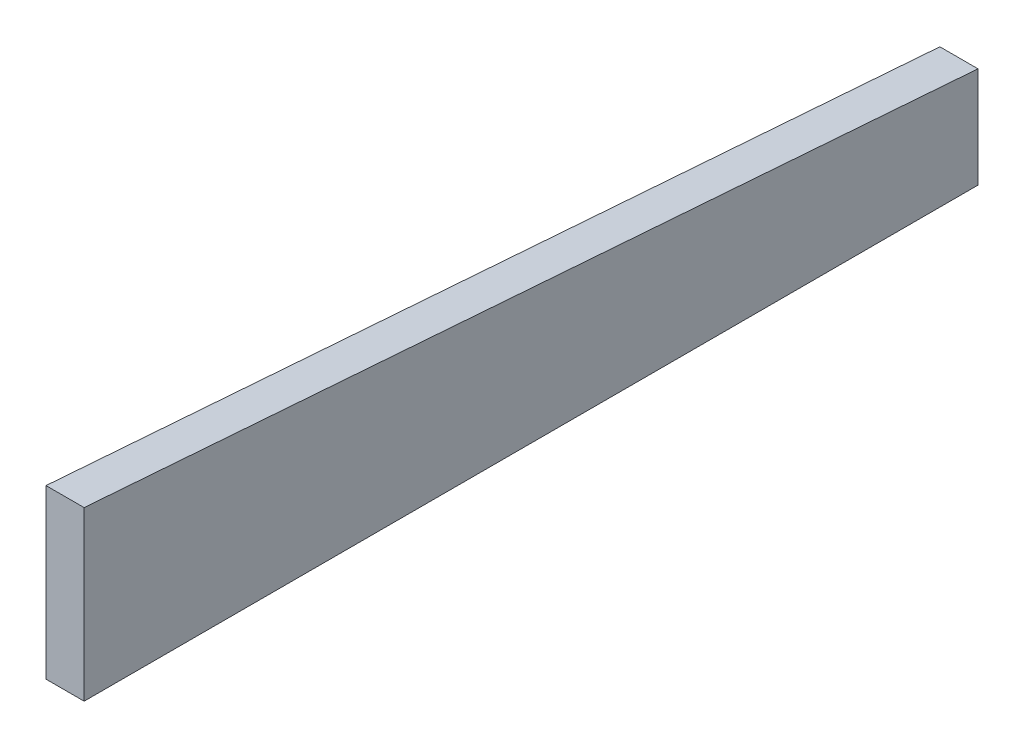
SolidWorks part; units mm, degrees
ref_plane "Front Plane" through (0, 0, 0) normal (0, 0, 1) x (1, 0, 0)
ref_plane "Top Plane" through (0, 0, 0) normal (0, 1, 0) x (1, 0, 0)
ref_plane "Right Plane" through (0, 0, 0) normal (1, 0, 0) x (0, 0, -1)
sketch "Sketch1" plane through (0, 0, 0) normal (1, 0, 0) x (0, 0, -1)
  line L0 (0, 0) -> (83.947, -6.2865)
  line L1 (83.947, -6.2865) -> (83.947, -15.748)
  line L2 (83.947, -15.748) -> (0, -15.748)
  line L3 (0, -15.748) -> (0, 0)
  dimension "D1" = 83.947
  dimension "D2" = 6.2865
  dimension "D3" = 15.748
extrude "Boss-Extrude1" add sketch "Sketch1" along normal blind 3.5814
